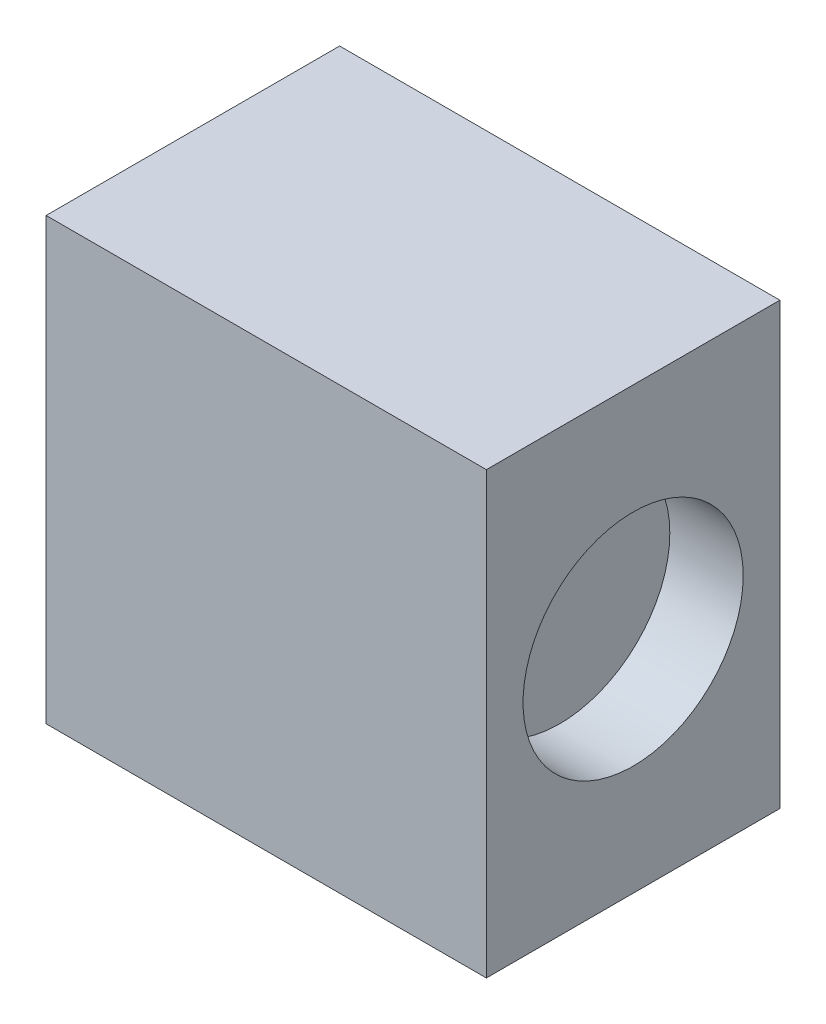
SolidWorks part; units mm, degrees
ref_plane "Спереди" through (0, 0, 0) normal (0, 0, 1) x (1, 0, 0)
ref_plane "Сверху" through (0, 0, 0) normal (0, 1, 0) x (1, 0, 0)
ref_plane "Справа" through (0, 0, 0) normal (1, 0, 0) x (0, 0, -1)
sketch "Sketch1" plane through (0, 0, 0) normal (0, 1, 0) x (1, 0, 0)
  line L1 (3, -2) -> (-3, -2)
  line L2 (3, -2) -> (3, 2)
  line L3 (3, 2) -> (-3, 2)
  line L4 (-3, -2) -> (-3, 2)
  line L5 (3, -2) -> (-3, 2) construction
  line L6 (3, 2) -> (-3, -2) construction
  point P0 (0, 0)
  dimension "D1" = 6
  dimension "D2" = 4
extrude "Boss-Extrude1" add sketch "Sketch1" along normal blind 6
sketch "Sketch2" plane through (3, 0, 0) normal (1, 0, 0) x (0, 0, -1)
  line L0 (0, 0) -> (0, 6) construction
  line L1 (-2, 0) -> (2, 0) construction
  line L2 (-2, 6) -> (2, 6) construction
  circle A0 centre (0, 3) radius 1.5
  dimension "D1" = 3
extrude "Cut-Extrude1" cut sketch "Sketch2" against normal blind 1
